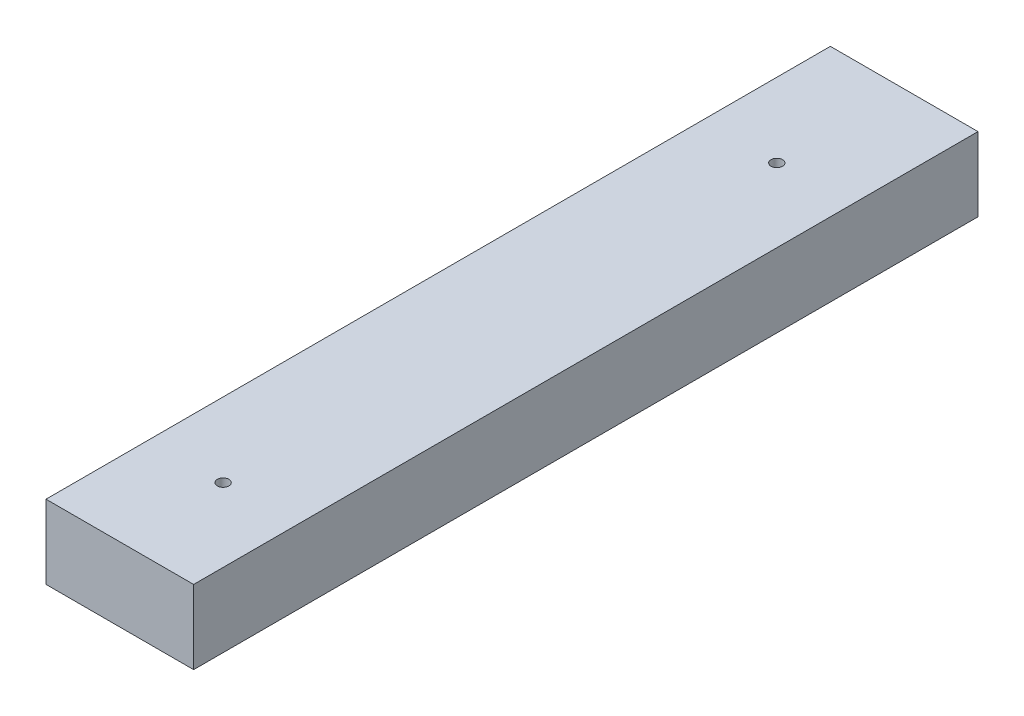
SolidWorks part; units mm, degrees
ref_plane "Front Plane" through (0, 0, 0) normal (0, 0, 1) x (1, 0, 0)
ref_plane "Top Plane" through (0, 0, 0) normal (0, 1, 0) x (1, 0, 0)
ref_plane "Right Plane" through (0, 0, 0) normal (1, 0, 0) x (0, 0, -1)
sketch "Sketch1" plane through (0, 0, 0) normal (0, 0, 1) x (1, 0, 0)
  line L1 (0, 0) -> (-101.6, 0)
  line L2 (0, 0) -> (0, 50.8)
  line L3 (0, 50.8) -> (-101.6, 50.8)
  line L4 (-101.6, 0) -> (-101.6, 50.8)
  dimension "D1" = 50.8
  dimension "D2" = 101.6
extrude "Boss-Extrude1" add sketch "Sketch1" along normal blind 539.75
sketch "Sketch2" plane through (0, 50.8, 0) normal (0, 1, 0) x (1, 0, 0)
  circle A0 centre (-50.5323, -87.9359) radius 3.9687
  circle A1 centre (-50.5323, -468.9359) radius 3.9688
  dimension "D2" = 7.9375
  dimension "D3" = 7.9375
  dimension "D1" = 381
extrude "Cut-Extrude1" cut sketch "Sketch2" against normal through all
